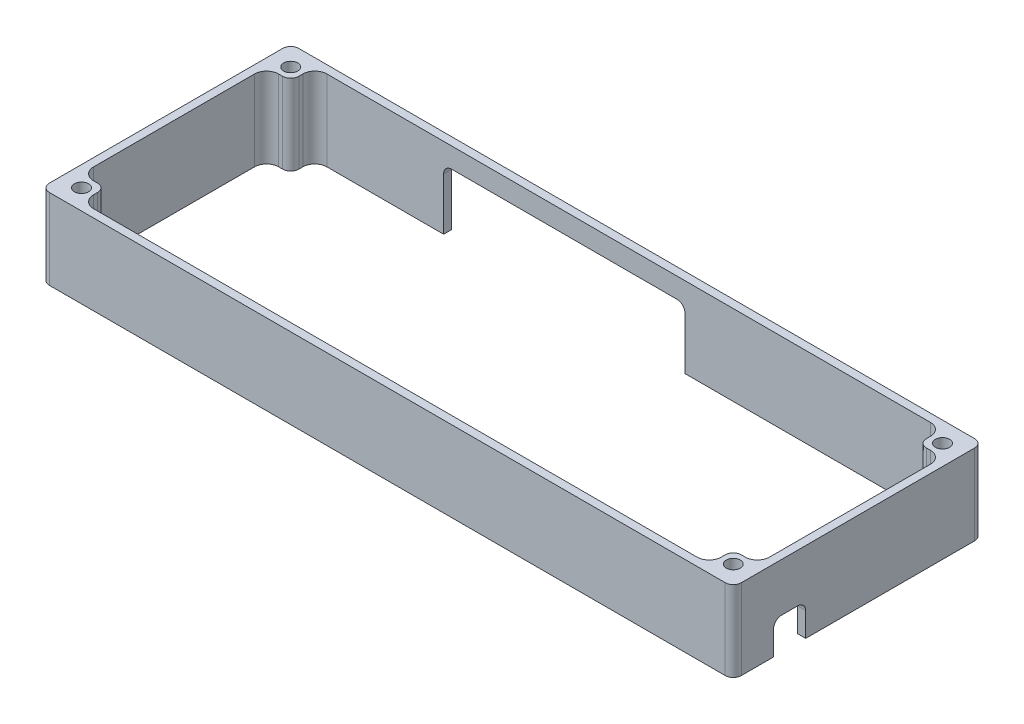
SolidWorks part; units mm, degrees
ref_plane "Front Plane" through (0, 0, 0) normal (0, 0, 1) x (1, 0, 0)
ref_plane "Top Plane" through (0, 0, 0) normal (0, 1, 0) x (1, 0, 0)
ref_plane "Right Plane" through (0, 0, 0) normal (1, 0, 0) x (0, 0, -1)
sketch "Sketch1" plane through (0, 0, 0) normal (0, 1, 0) x (1, 0, 0)
  line L0 (86, -29) -> (86, 29)
  line L1 (84, 31) -> (-84, 31)
  line L2 (-86, 29) -> (-86, -29)
  line L3 (-84, -31) -> (84, -31)
  line L4 (84, -23) -> (84, 23)
  line L5 (78, 29) -> (-78, 29)
  line L6 (-84, 23) -> (-84, -23)
  line L7 (-78, -29) -> (78, -29)
  line L8 (0, 0) -> (-96.1723, 0) construction
  line L9 (-84, -23) -> (-80, -23)
  line L12 (-78, -25) -> (-78, -29)
  line L13 (-84, -23) -> (-78, -29) construction
  line L14 (-84, -29) -> (-78, -23) construction
  line L15 (-84, 29) -> (-84, -29) construction
  line L16 (-84, -29) -> (84, -29) construction
  line L17 (-78, 25) -> (-78, 29)
  line L18 (-84, 23) -> (-80, 23)
  line L19 (0, 0) -> (0, 105.1923) construction
  line L20 (84, 29) -> (-84, 29) construction
  line L21 (78, 25) -> (78, 29)
  line L22 (84, 23) -> (80, 23)
  line L23 (78, -25) -> (78, -29)
  line L24 (84, -23) -> (80, -23)
  line L25 (84, -31) -> (-84, -31)
  line L26 (86, 29) -> (86, -29)
  line L27 (-84, 31) -> (84, 31)
  line L28 (-86, -29) -> (-86, 29)
  line L30 (84, -29) -> (84, 29) construction
  arc A0 (84, -31) -> (86, -29) centre (84, -29) ccw
  arc A1 (86, 29) -> (84, 31) centre (84, 29) ccw
  arc A2 (-84, 31) -> (-86, 29) centre (-84, 29) ccw
  arc A3 (-86, -29) -> (-84, -31) centre (-84, -29) ccw
  circle A4 centre (81, 26) radius 1.75
  circle A5 centre (81, -26) radius 1.75
  circle A6 centre (-81, -26) radius 1.75
  circle A7 centre (-81, 26) radius 1.75
  arc A8 (84, 29) -> (84, 29) centre (84, 29) ccw
  arc A9 (-84, 29) -> (-84, 29) centre (-84, 29) ccw
  arc A10 (-84, -29) -> (-84, -29) centre (-84, -29) ccw
  arc A11 (84, -29) -> (84, -29) centre (84, -29) ccw
  arc A12 (-80, -23) -> (-78, -25) centre (-80, -25) cw
  arc A13 (-80, 23) -> (-78, 25) centre (-80, 25) ccw
  arc A14 (80, 23) -> (78, 25) centre (80, 25) cw
  arc A15 (80, -23) -> (78, -25) centre (80, -25) ccw
  arc A16 (-84, -31) -> (-86, -29) centre (-84, -29) cw
  arc A17 (86, -29) -> (84, -31) centre (84, -29) cw
  arc A18 (84, 31) -> (86, 29) centre (84, 29) cw
  arc A19 (-86, 29) -> (-84, 31) centre (-84, 29) cw
  point P34 (-81, -26)
  dimension "D3" = 2
  dimension "D4" = 2
  dimension "D5" = 2
  dimension "D6" = 2
  dimension "D7" = 3.5
  dimension "D8" = 3.5
  dimension "D9" = 3.5
  dimension "D10" = 3.5
  dimension "D19" = 2
  dimension "D22" = 2
  dimension "D1" = 62
  dimension "D2" = 172
  dimension "D11" = 5
  dimension "D12" = 5
  dimension "D13" = 5
  dimension "D14" = 5
  dimension "D15" = 5
  dimension "D16" = 5
  dimension "D17" = 5
  dimension "D18" = 5
  dimension "D20" = 6
  dimension "D21" = 6
extrude "Boss-Extrude1" add sketch "Sketch1" along normal blind 20 contours L2 A3 L3 A0 L0 A1 L1 A2 A7 A6 A5 A4 L24 A15 L23 L7 L12 A12 L9 L6 L18 A13 L17 L5 L21 A14 L22 L4
sketch "Sketch2" plane through (0, 0, -31) normal (0, 0, -1) x (-1, 0, 0)
  line L0 (86, 20) -> (86, 0) construction
  line L1 (-12, 15) -> (44, 15)
  line L2 (-14, 13) -> (-14, -3)
  line L3 (-14, -3) -> (46, -3)
  line L4 (46, 13) -> (46, -3)
  line L5 (-14, 15) -> (46, -3) construction
  line L6 (-14, -3) -> (46, 15) construction
  line L7 (-84, 20) -> (84, 20) construction
  arc A0 (44, 15) -> (46, 13) centre (44, 13) cw
  arc A1 (-12, 15) -> (-14, 13) centre (-12, 13) ccw
  point P0 (16, 6)
  dimension "D4" = 2
  dimension "D1" = 40
  dimension "D2" = 60
  dimension "D3" = 5
  dimension "D5" = 18
extrude "Cut-Extrude1" cut sketch "Sketch2" against normal blind 20
fillet "Fillet1" radius 3 8 edges at (-78, 10, 29) (-84, 10, 23) (-84, 10, -23) (-78, 10, -29) (84, 10, 23) (78, 10, 29) (78, 10, -29) (84, 10, -23)
sketch "Sketch3" plane through (86, 0, 0) normal (1, 0, 0) x (0, 0, -1)
  line L0 (-29, 20) -> (29, 20) construction
  line L1 (-21, 20) -> (-13, 20)
  line L2 (-21, 20) -> (-21, 14) construction
  line L3 (-19, 12) -> (-15, 12) construction
  line L4 (-13, 20) -> (-13, 14) construction
  line L5 (-21, 20) -> (-13, 12) construction
  line L6 (-21, 12) -> (-13, 20) construction
  line L7 (-31, 20) -> (-31, 0) construction
  line L8 (1.4696, 10) -> (45.6757, 10) construction
  line L9 (-29, 0) -> (29, 0) construction
  line L10 (-13, 0) -> (-13, 6)
  line L11 (-19, 8) -> (-15, 8)
  line L12 (-21, 0) -> (-21, 6)
  line L13 (-21, 0) -> (-13, 0)
  arc A0 (-15, 12) -> (-13, 14) centre (-15, 14) ccw construction
  arc A1 (-21, 14) -> (-19, 12) centre (-19, 14) ccw construction
  arc A2 (-15, 8) -> (-13, 6) centre (-15, 6) cw
  arc A3 (-21, 6) -> (-19, 8) centre (-19, 6) cw
  point P0 (-17, 16)
  dimension "D4" = 2
  dimension "D1" = 8
  dimension "D2" = 8
  dimension "D3" = 10
extrude "Cut-Extrude5" cut sketch "Sketch3" against normal blind 10 contours L10 A2 L11 A3 L12 L13
